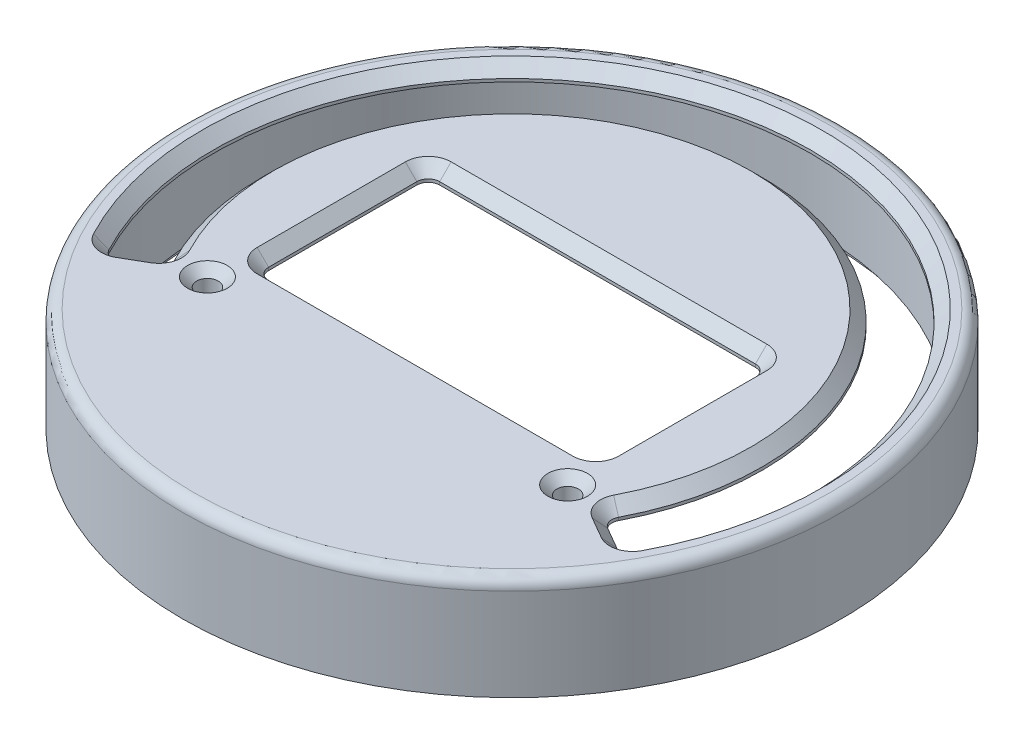
SolidWorks part; units mm, degrees
ref_plane "Front Plane" through (0, 0, 0) normal (0, 0, 1) x (1, 0, 0)
ref_plane "Top Plane" through (0, 0, 0) normal (0, 1, 0) x (1, 0, 0)
ref_plane "Right Plane" through (0, 0, 0) normal (1, 0, 0) x (0, 0, -1)
sketch "Sketch1" plane through (0, 0, 0) normal (0, 1, 0) x (1, 0, 0)
  line L0 (18.8, 9.5) -> (-18.8, -9.5) construction
  line L1 (20, -13.8201) -> (-20, -13.8201) construction
  line L2 (-28.7061, -16.5735) -> (-24.0868, -13.9065)
  line L3 (24.0868, -13.9065) -> (28.7061, -16.5735)
  line L4 (-28.7061, -16.5735) -> (28.7061, -16.5735) construction
  line L5 (0, 0) -> (0, -16.5735) construction
  line L6 (-24.0868, -13.9065) -> (0, 0) construction
  line L7 (0, 0) -> (24.0868, -13.9065) construction
  line L8 (-18.8, 9.5) -> (-18.8, -9.5)
  line L9 (-18.8, -9.5) -> (18.8, -9.5)
  line L10 (18.8, -9.5) -> (18.8, 9.5)
  line L11 (18.8, 9.5) -> (-18.8, 9.5)
  arc A0 (-22.3357, -16.5735) -> (22.3357, -16.5735) centre (0, 0) ccw construction
  circle A1 centre (0, 0) radius 36.5951
  arc A2 (28.7061, -16.5735) -> (-28.7061, -16.5735) centre (0, 0) ccw
  arc A3 (24.0868, -13.9065) -> (-24.0868, -13.9065) centre (0, 0) ccw
  arc A4 (-24.0868, -13.9065) -> (-22.3357, -16.5735) centre (0, 0) ccw construction
  arc A5 (22.3357, -16.5735) -> (24.0868, -13.9065) centre (0, 0) ccw construction
  arc A6 (-28.7061, -16.5735) -> (28.7061, -16.5735) centre (0, 0) ccw construction
  circle A7 centre (-20, -13.8201) radius 2.2225 construction
  circle A8 centre (20, -13.8201) radius 2.2225 construction
  circle A9 centre (0, 0) radius 34.1249 construction
  circle A10 centre (0, 0) radius 30.48 construction
  point P18 (0, -13.8201)
  point P21 (-26.3965, -15.24)
  dimension "D3" = 5.334
  dimension "D4" = 73.1901
  dimension "D7" = 4.445
  dimension "D10" = 68.2498
  dimension "D11" = 60.96
  dimension "D2" = 120
  dimension "D5" = 37.6
  dimension "D6" = 19
  dimension "D8" = 40
  dimension "D9" = 13.8201
extrude "Boss-Extrude1" add sketch "Sketch1" along normal blind 1.6
sketch "Sketch2" plane through (0, 0, 0) normal (0, -1, 0) x (1, 0, 0)
  circle A0 centre (20, 13.8201) radius 2.2225 construction
  circle A1 centre (-20, 13.8201) radius 2.2225 construction
  circle A2 centre (0, 0) radius 36.5951 construction
  circle A3 centre (0, 0) radius 34.1249 construction
  circle A4 centre (20, 13.8201) radius 2.2225
  circle A5 centre (-20, 13.8201) radius 2.2225
  circle A6 centre (0, 0) radius 36.5951
  circle A7 centre (0, 0) radius 34.1249
  circle M5 centre (0, 0) radius 36.5951
extrude "Boss-Extrude2" add sketch "Sketch2" along normal blind 8.3058 contours A5 | A4 | A7 M5
hole_wizard "CSK for M2 Flat Head Machine Screw1" positions "Sketch3" profile "Sketch4" countersink size "M2" standard "ANSI Metric" end condition up to next
sketch "Sketch3" plane through (0, 1.6, 0) normal (0, 1, 0) x (1, 0, 0)
  point P0 (-20, -13.8201)
  point P3 (20, -13.8201)
sketch "Sketch4" plane through (-20, 1.6, 13.8201) normal (1, 0, 0) x (0, 0, 1)
  line L0 (0, 0) -> (0, 9.9058)
  line L1 (0, 9.9058) -> (1.2, 9.9058)
  line L2 (1.2, 9.9058) -> (1.2, 1)
  line L3 (1.2, 1) -> (2.2, 0)
  line L5 (2.2, 0) -> (0, 0)
  line L6 (-1.2, 1) -> (-2.2, 0) construction
  line L11 (0, -6.35) -> (0, 107.95) construction
  dimension "Thru Hole Dia." = 2.4
  dimension "Thru Hole Depth" = 9.9058
  dimension "Near C'Sink Dia." = 4.4
  dimension "Near C'Sink Angle" = 90
fillet "Fillet1" radius 1.27 8 edges at (24.0868, 0.8, 13.9065) (28.7061, 0.8, 16.5735) (-28.7061, 0.8, 16.5735) (-24.0868, 0.8, 13.9065) (-18.8, 0.8, 9.5) (18.8, 0.8, 9.5) (18.8, 0.8, -9.5) (-18.8, 0.8, -9.5)
sketch "Sketch5" plane through (0, -8.3058, 0) normal (0, -1, 0) x (1, 0, 0)
  circle A1 centre (0, 0) radius 36.5951
  circle A2 centre (0, 0) radius 36.5951
  circle A3 centre (0, 0) radius 35.3949
  dimension "D2" = 70.7898
  dimension "D1" = 0
extrude "Boss-Extrude3" add sketch "Sketch5" along normal blind 1.6
chamfer "Chamfer2" distance 1.27 angle 45 16 edges at (0, 1.6, -27.813) (24.5783, 1.6, 13.7832) (-24.5783, 1.6, 13.7832) (26.3735, 1.6, 15.2267) (-26.3735, 1.6, 15.2267) (28.5725, 1.6, 16.0459) (-28.5725, 1.6, 16.0459) (0, 1.6, -33.147) (18.8, 1.6, 0) (18.428, 1.6, -9.128) (18.428, 1.6, 9.128) (0, 1.6, -9.5) (0, 1.6, 9.5) (-18.428, 1.6, 9.128) (-18.8, 1.6, 0) (-18.428, 1.6, -9.128)
fillet "Fillet2" radius 1.27 1 edges at (0, 1.6, 36.5951)
